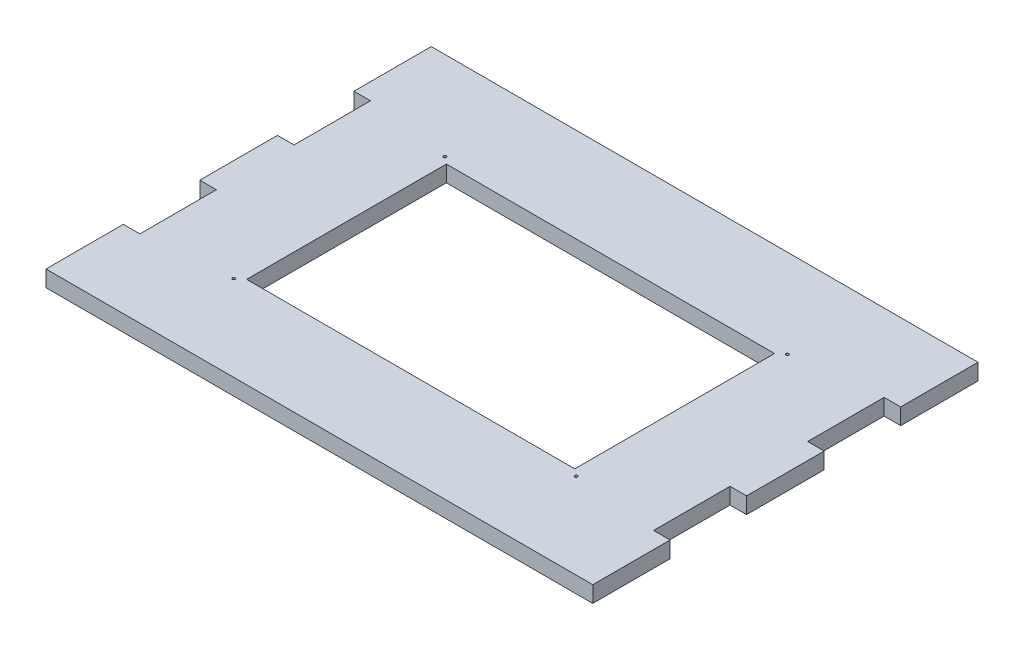
SolidWorks part; units mm, degrees
ref_plane "Front Plane" through (0, 0, 0) normal (0, 0, 1) x (1, 0, 0)
ref_plane "Top Plane" through (0, 0, 0) normal (0, 1, 0) x (1, 0, 0)
ref_plane "Right Plane" through (0, 0, 0) normal (1, 0, 0) x (0, 0, -1)
sketch "Sketch1" plane through (0, 0, 0) normal (0, 1, 0) x (1, 0, 0)
  line L0 (0, 0) -> (180, 0)
  line L1 (0, 100) -> (180, 100)
  line L2 (0, 0) -> (0, 100)
  line L4 (180, 0) -> (180, 100)
sketch "Sketch2" plane through (0, 0, 0) normal (0, 1, 0) x (1, 0, 0)
  line L1 (0, -6) -> (180, -6)
  line L2 (0, -6) -> (0, 106)
  line L3 (0, 106) -> (180, 106)
  line L4 (180, -6) -> (180, 106)
sketch "Sketch3" plane through (0, 0, 0) normal (0, 1, 0) x (1, 0, 0)
  line L1 (-6, -14) -> (186, -14)
  line L2 (-6, -14) -> (-6, 121)
  line L3 (-6, 121) -> (186, 121)
  line L4 (186, -14) -> (186, 121)
extrude "Boss-Extrude1" add sketch "Sketch3" along normal blind 5.7
ref_plane "Plane1" through (0, 5.7, 0) normal (0, 1, 0) x (1, 0, 0)
sketch "Sketch5" plane through (0, 5.7, 0) normal (0, 1, 0) x (1, 0, 0)
  line L0 (0, 0) -> (180, 0)
  line L1 (0, 100) -> (180, 100)
  line L2 (0, 0) -> (0, 100)
  line L4 (180, 0) -> (180, 100)
sketch "Sketch7" plane through (0, 5.7, 0) normal (0, 1, 0) x (1, 0, 0)
  line L1 (0, -6) -> (180, -6)
  line L2 (0, -6) -> (0, 106)
  line L3 (0, 106) -> (180, 106)
  line L4 (180, -6) -> (180, 106)
sketch "Sketch8" plane through (0, 0, 0) normal (0, 1, 0) x (1, 0, 0)
  line L4 (35, 23) -> (145, 23)
  line L5 (35, 23) -> (35, 83)
  line L6 (35, 83) -> (145, 83)
  line L7 (145, 23) -> (145, 83)
  line L8 (35, 23) -> (145, 83) construction
  line L9 (35, 83) -> (145, 23) construction
  point P6 (90, 53)
  point P7 (90, 53)
sketch "Sketch9" plane through (0, 0, 0) normal (0, 1, 0) x (1, 0, 0)
  line L1 (32.5, 88) -> (147.5, 88)
  line L2 (32.5, 88) -> (32.5, 18)
  line L3 (32.5, 18) -> (147.5, 18)
  line L4 (147.5, 88) -> (147.5, 18)
  line L5 (32.5, 88) -> (147.5, 18) construction
  line L6 (32.5, 18) -> (147.5, 88) construction
  point P0 (90, 53)
sketch "Sketch10" plane through (0, 0, 0) normal (0, 1, 0) x (1, 0, 0)
  line L1 (27, 93) -> (153, 93)
  line L2 (27, 93) -> (27, 13)
  line L3 (27, 13) -> (153, 13)
  line L4 (153, 93) -> (153, 13)
  line L5 (27, 93) -> (153, 13) construction
  line L6 (27, 13) -> (153, 93) construction
  point P0 (90, 53)
extrude "Cut-Extrude2" cut sketch "Sketch9" along normal blind 47
sketch "Sketch12" plane through (0, 0, 0) normal (0, 1, 0) x (1, 0, 0)
  line L1 (30, 90) -> (150, 90) construction
  line L2 (30, 90) -> (30, 16) construction
  line L3 (30, 16) -> (150, 16) construction
  line L4 (150, 90) -> (150, 16) construction
  line L5 (30, 90) -> (150, 16) construction
  line L6 (30, 16) -> (150, 90) construction
  circle A0 centre (30, 90) radius 0.5
  circle A2 centre (30, 16) radius 0.5
  circle A4 centre (150, 16) radius 0.5
  circle A6 centre (150, 90) radius 0.5
  point P0 (90, 53)
extrude "Cut-Extrude3" cut sketch "Sketch12" along normal blind 37
sketch "Sketch13" plane through (0, 0, 0) normal (0, 1, 0) x (1, 0, 0)
  line L0 (-5.8, 121) -> (-5.8, 93.9)
  line L2 (-5.8, 93.9) -> (0, 93.9)
  line L4 (0, 93.9) -> (0, 67.1)
  line L5 (0, 67.1) -> (-5.8, 67.1)
  line L6 (-5.8, 67.1) -> (-5.8, 39.9)
  line L7 (-5.8, 39.9) -> (0, 39.9)
  line L8 (0, 39.9) -> (0, 13.1)
  line L9 (0, 13.1) -> (-5.8, 13.1)
  line L10 (-5.8, 13.1) -> (-5.8, -14)
  line L11 (-5.8, -14) -> (-9.8, -14)
  line L12 (-9.8, -14) -> (-9.8, 121)
  line L13 (-9.8, 121) -> (-5.8, 121)
  line L14 (90, 131) -> (90, -20) construction
  line L15 (189.8, 121) -> (185.8, 121)
  line L16 (189.8, -14) -> (189.8, 121)
  line L17 (185.8, -14) -> (189.8, -14)
  line L18 (185.8, 13.1) -> (185.8, -14)
  line L19 (180, 13.1) -> (185.8, 13.1)
  line L20 (180, 39.9) -> (180, 13.1)
  line L21 (185.8, 39.9) -> (180, 39.9)
  line L22 (185.8, 67.1) -> (185.8, 39.9)
  line L23 (180, 67.1) -> (185.8, 67.1)
  line L24 (180, 93.9) -> (180, 67.1)
  line L25 (185.8, 93.9) -> (180, 93.9)
  line L26 (185.8, 121) -> (185.8, 93.9)
extrude "Cut-Extrude4" cut sketch "Sketch13" along normal blind 11
